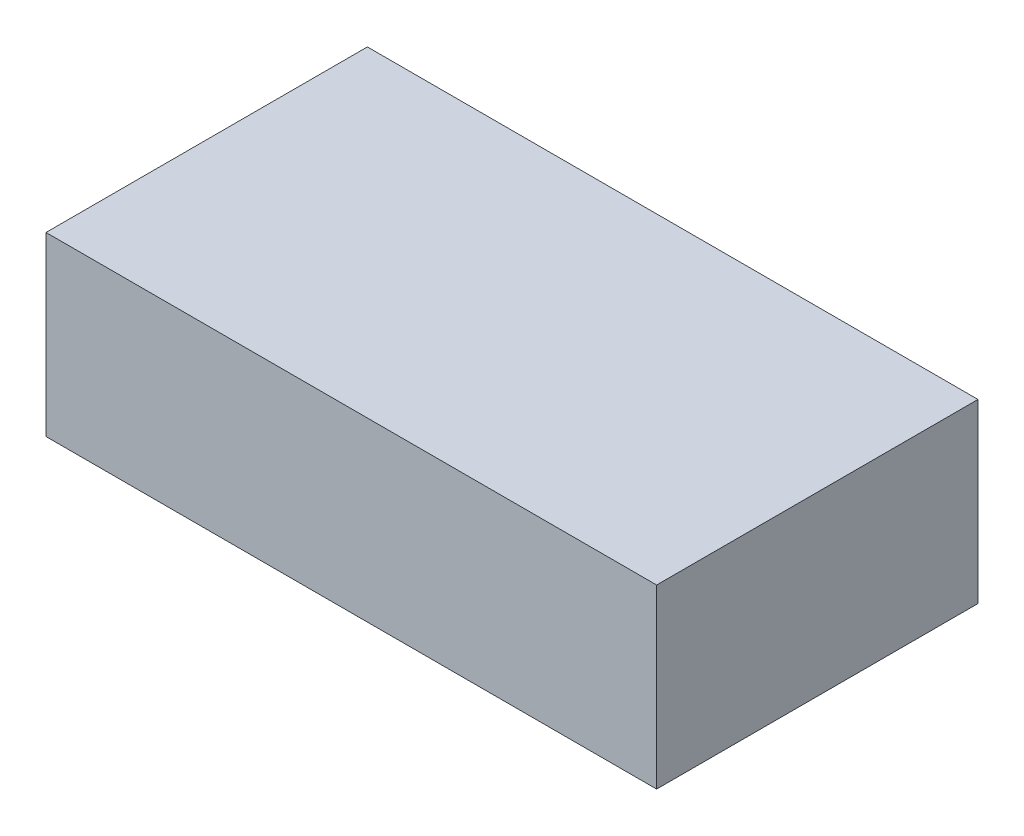
SolidWorks part; units mm, degrees
ref_plane "Plan de face" through (0, 0, 0) normal (0, 0, 1) x (1, 0, 0)
ref_plane "Plan de dessus" through (0, 0, 0) normal (0, 1, 0) x (1, 0, 0)
ref_plane "Plan de droite" through (0, 0, 0) normal (1, 0, 0) x (0, 0, -1)
sketch "Esquisse1" plane through (0, 0, 0) normal (0, 1, 0) x (1, 0, 0)
  line L1 (0, 0) -> (-76, 0)
  line L2 (0, 0) -> (0, -40)
  line L3 (0, -40) -> (-76, -40)
  line L4 (-76, 0) -> (-76, -40)
  dimension "D1" = 76
  dimension "D2" = 40
extrude "Boss.-Extru.1" add sketch "Esquisse1" along normal blind 22
